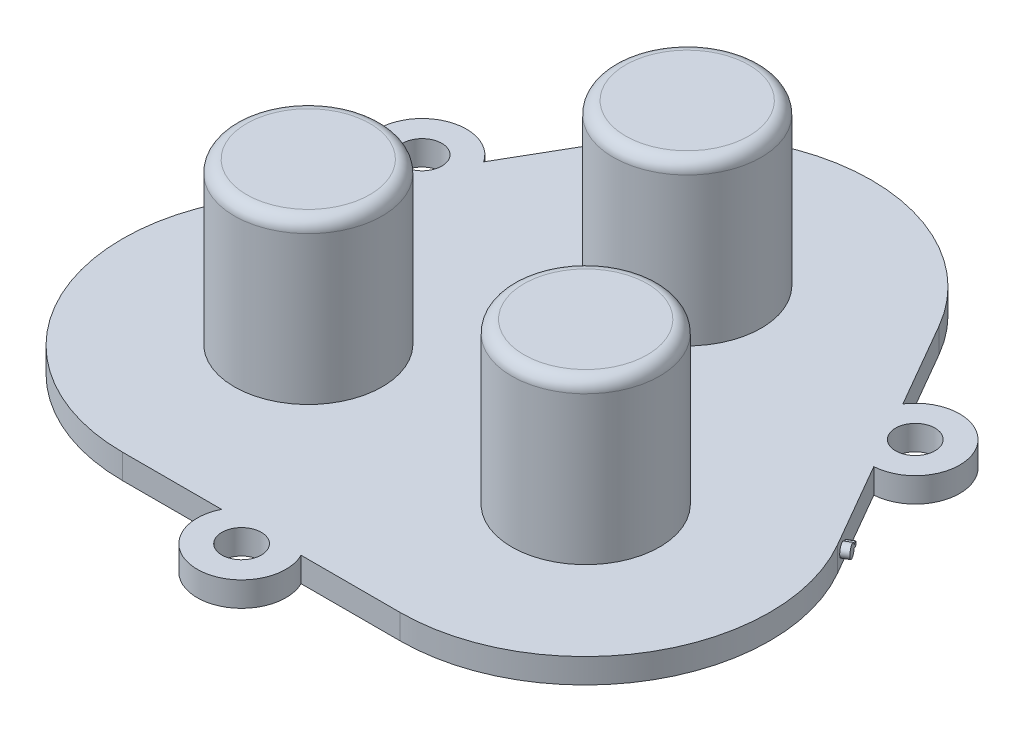
SolidWorks part; units mm, degrees
ref_plane "Front Plane" through (0, 0, 0) normal (0, 0, 1) x (1, 0, 0)
ref_plane "Top Plane" through (0, 0, 0) normal (0, 1, 0) x (1, 0, 0)
ref_plane "Right Plane" through (0, 0, 0) normal (1, 0, 0) x (0, 0, -1)
sketch "Sketch5" plane through (0, 0, 0) normal (0, 1, 0) x (1, 0, 0)
  line L3 (-11.25, -22.1428) -> (-3.2249, -22.1428)
  line L4 (3.2249, -22.1428) -> (11.25, -22.1428)
  line L5 (24.2404, 0.3572) -> (20.2278, 7.3072)
  line L6 (17.0029, 12.8928) -> (12.9904, 19.8428)
  line L7 (-12.9904, 19.8428) -> (-17.0029, 12.8928)
  line L8 (-20.2278, 7.3072) -> (-24.2404, 0.3572)
  arc A3 (-3.2249, -22.1428) -> (3.2249, -22.1428) centre (0, -23.7428) ccw
  arc A4 (11.25, -22.1428) -> (24.2404, 0.3572) centre (11.25, -7.1428) ccw
  arc A5 (20.2278, 7.3072) -> (17.0029, 12.8928) centre (20.001, 10.9) ccw
  arc A6 (12.9904, 19.8428) -> (-12.9904, 19.8428) centre (0, 12.3428) ccw
  arc A7 (-17.0029, 12.8928) -> (-20.2278, 7.3072) centre (-20.001, 10.9) ccw
  arc A8 (-24.2404, 0.3572) -> (-11.25, -22.1428) centre (-11.25, -7.1428) ccw
  circle A9 centre (20.001, 10.9) radius 1.6
  circle A10 centre (0, -23.7428) radius 1.6
  circle A11 centre (-20.001, 10.9) radius 1.6
extrude "Boss-Extrude2" add sketch "Sketch5" along normal blind 2
sketch "Sketch6" plane through (0, 0, 0) normal (0, 1, 0) x (1, 0, 0)
  circle A12 centre (-0.06, 12.4628) radius 6
  circle A13 centre (11.19, -7.0227) radius 6
  circle A14 centre (-11.31, -7.0227) radius 6
extrude "Boss-Extrude3" add sketch "Sketch6" along normal blind 15
fillet "Fillet1" radius 1 3 edges at (-11.31, 15, 13.0227) (11.19, 15, 13.0227) (-0.06, 15, -6.4628)
sketch "Sketch7" plane through (18.335, 0, -10.5857) normal (0.866, 0, -0.5) x (-0.5, 0, -0.866)
  arc A0 (-10.342, 1.0528) -> (-10.342, 0.9472) centre (-10.8392, 1) ccw
  arc A1 (-10.342, 0.9472) -> (-10.342, 1.0528) centre (-10.1491, 1) ccw
  point P4 (-10.0456, 1)
  point P5 (-9.9163, 1)
  point P6 (0, 0)
  point P7 (0, 0)
  point P8 (-10.0158, 1)
  point P9 (-10.1491, 1)
  dimension "D1" = 1
  dimension "D2" = 0.4
extrude "Boss-Extrude5" add sketch "Sketch7" along normal blind 0.6
